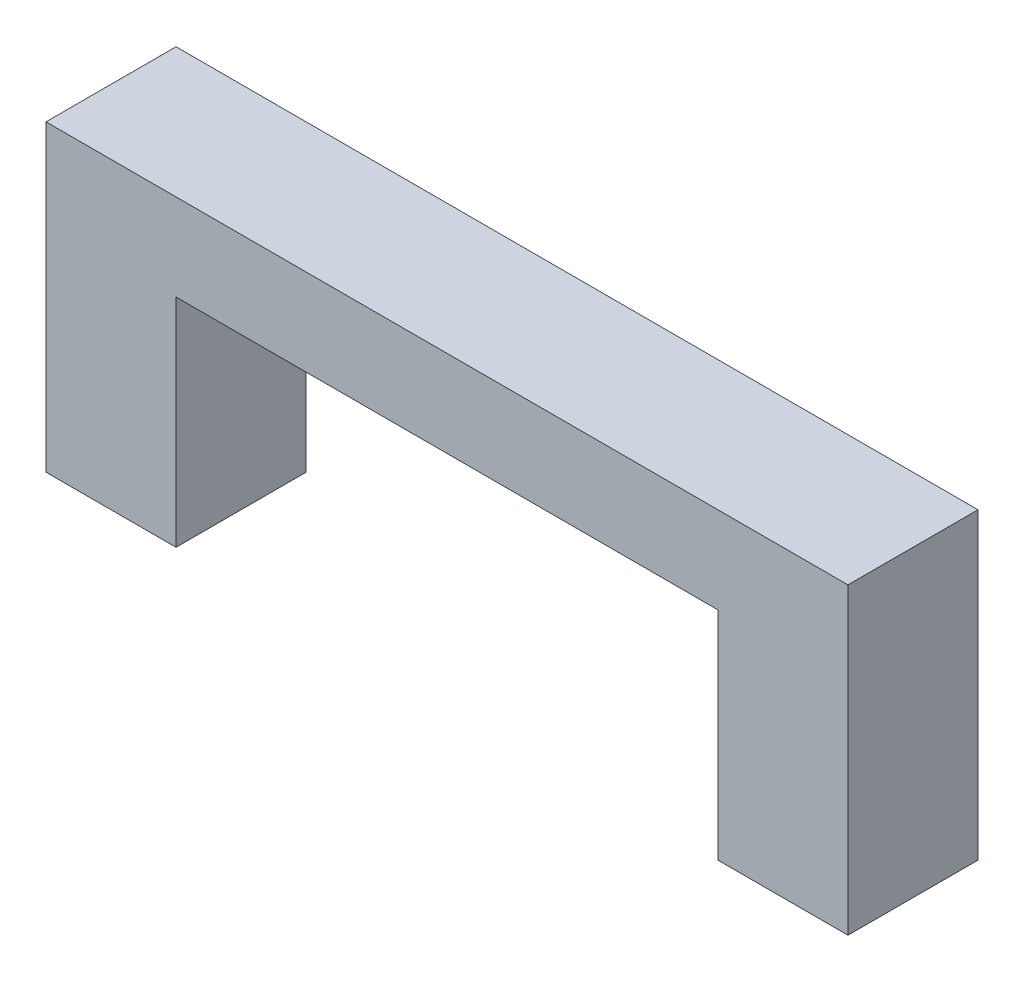
SolidWorks part; units mm, degrees
ref_plane "Front Plane" through (0, 0, 0) normal (0, 0, 1) x (1, 0, 0)
ref_plane "Top Plane" through (0, 0, 0) normal (0, 1, 0) x (1, 0, 0)
ref_plane "Right Plane" through (0, 0, 0) normal (1, 0, 0) x (0, 0, -1)
sketch "Sketch1" plane through (0, 0, 0) normal (0, 0, 1) x (1, 0, 0)
  line L0 (0, 0) -> (0, 7)
  line L1 (0, 7) -> (18.5, 7)
  line L2 (18.5, 7) -> (18.5, 0)
  line L3 (18.5, 0) -> (15.5, 0)
  line L4 (15.5, 0) -> (15.5, 5)
  line L5 (15.5, 5) -> (3, 5)
  line L6 (3, 5) -> (3, 0)
  line L7 (3, 0) -> (0, 0)
  point P9 (1.5, 0)
  point P10 (17, 0)
  dimension "D1" = 3
  dimension "D2" = 5
  dimension "D3" = 7
  dimension "D4" = 15.5
extrude "Boss-Extrude1" add sketch "Sketch1" along normal blind 3
sketch "Sketch2" plane through (0, 0, 0) normal (0, -1, 0) x (1, 0, 0)
  line L0 (3, 3) -> (3, 0) construction
  line L1 (0.75, 2.25) -> (2.25, 2.25)
  line L2 (0.75, 2.25) -> (0.75, 0.75)
  line L3 (0.75, 0.75) -> (2.25, 0.75)
  line L4 (2.25, 2.25) -> (2.25, 0.75)
  line L5 (0.75, 2.25) -> (2.25, 0.75) construction
  line L6 (0.75, 0.75) -> (2.25, 2.25) construction
  line L7 (16.25, 2.25) -> (17.75, 2.25)
  line L8 (16.25, 2.25) -> (16.25, 0.75)
  line L9 (16.25, 0.75) -> (17.75, 0.75)
  line L10 (17.75, 2.25) -> (17.75, 0.75)
  line L11 (16.25, 2.25) -> (17.75, 0.75) construction
  line L12 (16.25, 0.75) -> (17.75, 2.25) construction
  line L13 (0, 3) -> (3, 3) construction
  line L14 (18.5, 3) -> (18.5, 0) construction
  line L15 (15.5, 3) -> (18.5, 3) construction
  point P4 (1.5, 1.5)
  point P9 (17, 1.5)
  point P12 (3, 1.5)
  point P15 (1.5, 3)
  point P16 (0, 0)
  point P19 (18.5, 1.5)
  point P22 (0, 0)
  point P23 (17, 3)
  dimension "D1" = 1.5
extrude "Cut-Extrude1" cut sketch "Sketch2" against normal blind 2 contours L10 L7 L8 L9 | L1 L4 L3 L2
